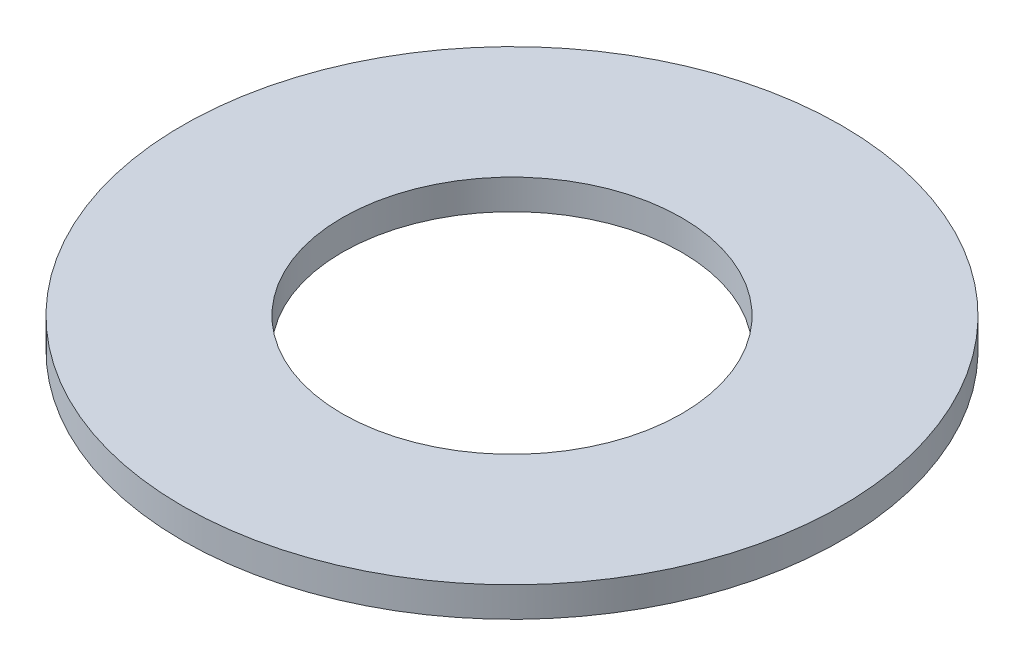
SolidWorks part; units mm, degrees
ref_plane "Спереди" through (0, 0, 0) normal (0, 0, 1) x (1, 0, 0)
ref_plane "Сверху" through (0, 0, 0) normal (0, 1, 0) x (1, 0, 0)
ref_plane "Справа" through (0, 0, 0) normal (1, 0, 0) x (0, 0, -1)
sketch "Эскиз1" plane through (0, 0, 0) normal (1, 0, 0) x (0, 0, -1)
  line L0 (0, 0) -> (0, 27.8338) construction
  line L1 (8.5, 0) -> (16.5, 0)
  line L2 (8.5, 0) -> (8.5, 1.5)
  line L3 (8.5, 1.5) -> (16.5, 1.5)
  line L4 (16.5, 0) -> (16.5, 1.5)
  dimension "D1" = 8.5
  dimension "D2" = 1.5
  dimension "D3" = 8
revolve "Повернуть1" add sketch "Эскиз1" angle 360 about L0
